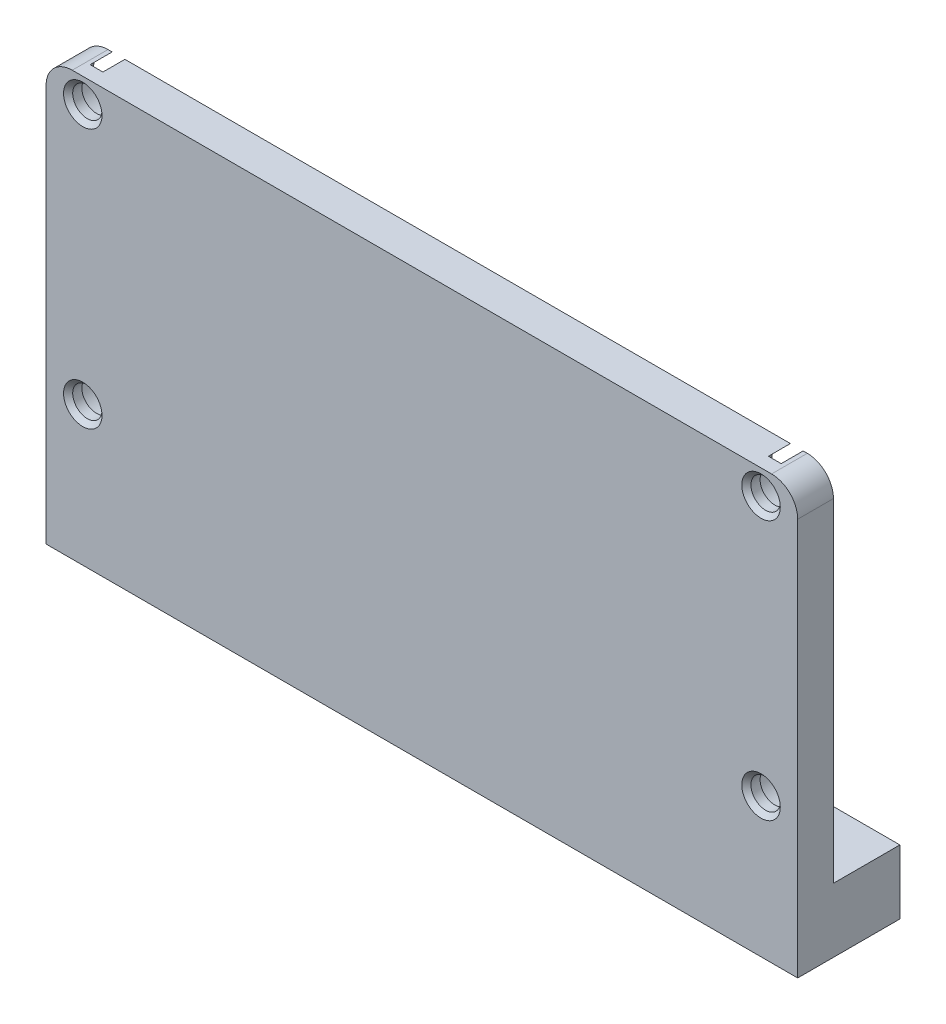
SolidWorks part; units mm, degrees
ref_plane "Front Plane" through (0, 0, 0) normal (0, 0, 1) x (1, 0, 0)
ref_plane "Top Plane" through (0, 0, 0) normal (0, 1, 0) x (1, 0, 0)
ref_plane "Right Plane" through (0, 0, 0) normal (1, 0, 0) x (0, 0, -1)
sketch "Sketch1" plane through (0, 0, 0) normal (0, 0, 1) x (1, 0, 0)
  line L1 (81, 11.6) -> (1, 11.6) construction
  line L3 (0, -35.2) -> (82, -35.2)
  line L5 (79.15, 11.6) -> (2.85, 11.6)
  line L9 (82, -35.2) -> (82, 8.75)
  line L10 (0, 8.75) -> (0, -35.2)
  line L11 (4, 8.9396) -> (4, -41.6656) construction
  circle A0 centre (4, 8.9396) radius 1.6 construction
  circle A1 centre (78, 8.9396) radius 1.6 construction
  circle A2 centre (4, -29.89) radius 1.6 construction
  circle A3 centre (4, 8.9396) radius 1.6
  circle A4 centre (78, 8.9396) radius 1.6
  arc A5 (82, 8.75) -> (79.15, 11.6) centre (79.15, 8.75) ccw
  arc A6 (0, 8.75) -> (2.85, 11.6) centre (2.85, 8.75) cw
  dimension "D1" = 46.8
  dimension "D2" = 2.85
extrude "Boss-Extrude1" add sketch "Sketch1" along normal blind 11.15 contours A3
sketch "Sketch2" plane through (0, 0, 0) normal (0, 0, -1) x (-1, 0, 0)
  line L0 (0, -49.6) -> (-82, -49.6) construction
  line L1 (0, -49.6) -> (-82, -49.6) construction
  line L2 (-82, -54.6) -> (0, -54.6)
  line L3 (-82, -34.6) -> (0, -34.6)
  line L4 (-82, -35.2) -> (-82, 8.75) construction
  line L5 (0, 8.75) -> (0, -35.2) construction
  line L7 (0, -34.6) -> (0, -35.2)
  line L8 (-82, -35.2) -> (-82, -34.6)
  line L9 (-82, -35.2) -> (0, -35.2)
  dimension "D1" = 5
  dimension "D2" = 20
extrude "Cut-Extrude1" cut sketch "Sketch2" against normal blind 8 contours L3 L7 L9 L8
sketch "Sketch3" plane through (0, -34.6, 0) normal (0, -1, 0) x (1, 0, 0)
  line L0 (10.85, 4) -> (10.85, 0)
  line L1 (14.15, 4) -> (14.15, 0)
  line L2 (16.75, 4) -> (16.75, 0)
  line L3 (23.25, 4) -> (23.25, 0)
  line L4 (0, 0) -> (82, 0)
  line L5 (82, 0) -> (82, 8)
  line L6 (82, 8) -> (0, 8)
  line L7 (0, 8) -> (0, 0)
  line L8 (10.85, 0) -> (14.15, 0)
  line L9 (82, 0) -> (82, 8)
  line L10 (82, 8) -> (0, 8)
  line L11 (0, 8) -> (0, 0)
  line L12 (25.85, 4) -> (25.85, 0)
  line L13 (29.15, 4) -> (29.15, 0)
  line L14 (25.85, 0) -> (82, 0)
  line L15 (16.75, 0) -> (23.25, 0)
  arc A0 (14.15, 4) -> (10.85, 4) centre (12.5, 4) ccw
  arc A1 (23.25, 4) -> (16.75, 4) centre (20, 4) ccw
  arc A2 (29.15, 4) -> (25.85, 4) centre (27.5, 4) ccw
  line M5 (0, 0) -> (82, 0)
  dimension "D2" = 3.3
  dimension "D3" = 3.3
  dimension "D4" = 15
  dimension "D5" = 7.5
  dimension "D6" = 6.5
  dimension "D7" = 20
  dimension "D1" = 0
extrude "Cut-Extrude2" cut sketch "Sketch3" against normal up to next (46.2 mm away) contours L13 A2 L12 M5 | A0 L0 L8 L1 | A1 L2 L15 L3
sketch "Sketch4" plane through (0, 11.6, 0) normal (0, 1, 0) x (1, 0, 0)
  line L0 (9.25, -4) -> (9.25, 0)
  line L1 (10.85, 0) -> (2.85, 0) construction
  line L2 (15.75, -4) -> (15.75, 0)
  line L3 (16.75, 0) -> (14.15, 0) construction
  line L4 (15.75, 0) -> (9.25, 0)
  line L5 (24.25, -4) -> (24.25, 0)
  line L6 (25.85, 0) -> (23.25, 0) construction
  line L7 (24.25, 0) -> (30.75, 0)
  line L8 (79.15, 0) -> (29.15, 0) construction
  line L9 (30.75, 0) -> (30.75, -4)
  arc A0 (10.85, -4) -> (14.15, -4) centre (12.5, -4) ccw construction
  arc A1 (25.85, -4) -> (29.15, -4) centre (27.5, -4) ccw construction
  arc A2 (10.85, -4) -> (14.15, -4) centre (12.5, -4) ccw construction
  arc A3 (25.85, -4) -> (29.15, -4) centre (27.5, -4) ccw construction
  arc A4 (9.25, -4) -> (15.75, -4) centre (12.5, -4) ccw
  arc A5 (24.25, -4) -> (30.75, -4) centre (27.5, -4) ccw
  dimension "D1" = 6.5
  dimension "D2" = 6.5
extrude "Cut-Extrude3" cut sketch "Sketch4" against normal offset from surface (40.2 mm away) 6 up to face at (25.25, -34.6, 2.9094)
sketch "Sketch6" plane through (0, 11.6, 0) normal (0, 1, 0) x (1, 0, 0)
  line L0 (15.75, -4) -> (15.75, 0) construction
  line L1 (24.25, 0) -> (24.25, -4) construction
  line L2 (15.75, -4) -> (15.75, 0)
  line L3 (24.25, 0) -> (24.25, -4)
  line L4 (12.5, -7.25) -> (0, -7.25)
  line L6 (0, -7.25) -> (0, 1.0612)
  line L7 (0, 1.0612) -> (15.75, 1.0612)
  line L8 (15.75, 1.0612) -> (15.75, 0)
  line L9 (27.5, -7.25) -> (41, -7.25)
  line L10 (41, -7.25) -> (41, 0)
  line L11 (79.15, 0) -> (30.75, 0) construction
  line L12 (41, 0) -> (24.25, 0)
  arc A0 (9.25, -4) -> (15.75, -4) centre (12.5, -4) ccw construction
  arc A1 (24.25, -4) -> (30.75, -4) centre (27.5, -4) ccw construction
  arc A2 (12.5, -7.25) -> (15.75, -4) centre (12.5, -4) ccw
  arc A3 (24.25, -4) -> (27.5, -7.25) centre (27.5, -4) ccw
  dimension "D1" = 41
extrude "Cut-Extrude5" cut sketch "Sketch6" against normal offset from surface (39.2 mm away) 7 up to face at (25.25, -34.6, 2.9094)
ref_plane "Plane1" through (41, 0, 0) normal (-1, 0, 0) x (0, 0, 1)
mirror "Mirror1" about plane through (41, 0, 0) normal (-1, 0, 0) of "Cut-Extrude5", "Cut-Extrude3", "Cut-Extrude2", "Cut-Extrude1"
sketch "Sketch8" plane through (0, 0, 8) normal (0, 0, -1) x (-1, 0, 0)
  line L4 (-82, -34.6) -> (-82, -35.2)
  line L5 (-82, -35.2) -> (0, -35.2)
  line L6 (0, -35.2) -> (0, -34.6)
  line L7 (0, -34.6) -> (-82, -34.6)
  line L8 (-82, -34.6) -> (-82, -35.2)
  line L9 (-82, -35.2) -> (0, -35.2)
  line L10 (0, -35.2) -> (0, -34.6)
  line L11 (0, -34.6) -> (-82, -34.6)
  dimension "D1" = 0
sketch "Sketch9" plane through (0, 0, 0) normal (-1, 0, 0) x (0, 0, 1)
  line L2 (7.25, 11.6) -> (0, 2.4)
  line L3 (0, 11.6) -> (7.25, 11.6)
sketch "Sketch12" plane through (0, 11.6, 0) normal (0, 1, 0) x (1, 0, 0)
  line L0 (16.75, -4) -> (16.75, 0)
  line L1 (16.75, 0) -> (18, 0)
  line L2 (23.25, 0) -> (23.25, -4)
  line L5 (22, 0) -> (23.25, 0)
  line L6 (58.75, -4) -> (58.75, 0)
  line L7 (58.75, 0) -> (60.05, 0)
  line L8 (65.25, 0) -> (65.25, -4) construction
  line L9 (65.25, 0) -> (65.25, -4)
  line L10 (60.05, 0) -> (60.155, -3.1064)
  line L11 (18, 0) -> (18.11, -3.0846)
  line L12 (63.95, 0) -> (65.25, 0)
  line L13 (22, 0) -> (21.89, -3.0846)
  line L15 (63.95, 0) -> (63.845, -3.1064)
  arc A0 (16.75, -4) -> (23.25, -4) centre (20, -4) ccw construction
  arc A1 (58.75, -4) -> (65.25, -4) centre (62, -4) ccw construction
  arc A2 (16.75, -4) -> (23.25, -4) centre (20, -4) ccw
  arc A3 (58.75, -4) -> (65.25, -4) centre (62, -4) ccw
  arc A4 (18.11, -3.0846) -> (21.89, -3.0846) centre (20, -4) ccw
  arc A5 (60.155, -3.1064) -> (63.845, -3.1064) centre (62, -4) ccw
  dimension "D1" = 1.25
  dimension "D2" = 4.1
  dimension "D3" = 1.3
  dimension "D4" = 1.3
  dimension "D5" = 1.25
extrude "Boss-Extrude2" add sketch "Sketch12" against normal offset from surface (32.2 mm away) 7 up to face at (41, -27.6, 3.9744)
chamfer "Chamfer3" distance 1.1 angle 45 3 edges at (58.75, -20.6, 2) (65.25, -20.6, 2) (62, -20.6, 7.25)
chamfer "Chamfer4" distance 1.1 angle 45 3 edges at (16.75, -20.6, 2) (23.25, -20.6, 2) (20, -20.6, 7.25)
extrude "Cut-Extrude12" cut sketch "Sketch9" against normal through all and the other way through all flip side to cut contours L3 L2
fillet "Fillet3" radius 15 2 edges at (16.875, 2.4, 0) (23.125, 2.4, 0)
sketch "Sketch13" plane through (0, 0, 7.25) normal (0, 0, -1) x (-1, 0, 0)
  circle A0 centre (-78, 8.9396) radius 2.85
  dimension "D1" = 5.7
sketch "Sketch14" plane through (0, 0, 11.15) normal (0, 0, 1) x (1, 0, 0)
  circle A0 centre (4, -19.4004) radius 1.6 construction
  circle A1 centre (4, -19.4004) radius 1.6
extrude "Cut-Extrude14" cut sketch "Sketch14" against normal through all contours A1
mirror "Mirror3" about plane through (41, 0, 0) normal (-1, 0, 0) of "Cut-Extrude14"
sketch "Sketch18" plane through (0, -27.6, 0) normal (0, 1, 0) x (1, 0, 0)
  line L6 (14.15, 0) -> (14.15, -4)
  line L7 (10.85, -4) -> (10.85, 0)
  line L8 (10.85, 0) -> (9.25, 0)
  line L9 (9.25, 0) -> (9.25, -4)
  line L10 (15.75, -4) -> (15.75, 0)
  line L11 (15.75, 0) -> (14.15, 0)
  line L12 (14.15, 0) -> (14.15, -1.2)
  line L13 (10.85, -1.2) -> (10.85, 0)
  line L14 (10.85, 0) -> (9.25, 0)
  line L15 (9.25, 0) -> (9.25, -4)
  line L16 (15.75, -4) -> (15.75, 0)
  line L17 (15.75, 0) -> (14.15, 0)
  line L18 (29.15, 0) -> (29.15, -4)
  line L19 (25.85, -4) -> (25.85, 0)
  line L20 (25.85, 0) -> (24.25, 0)
  line L21 (24.25, 0) -> (24.25, -4)
  line L22 (30.75, -4) -> (30.75, 0)
  line L23 (30.75, 0) -> (29.15, 0)
  line L24 (29.15, 0) -> (29.15, -1.2)
  line L25 (25.85, -1.2) -> (25.85, 0)
  line L26 (25.85, 0) -> (24.25, 0)
  line L27 (24.25, 0) -> (24.25, -4)
  line L28 (30.75, -4) -> (30.75, 0)
  line L29 (30.75, 0) -> (29.15, 0)
  arc A0 (10.85, -1.2) -> (9.25, -4) centre (12.5, -4) ccw
  arc A1 (15.75, -4) -> (14.15, -1.2) centre (12.5, -4) ccw
  arc A2 (10.85, -4) -> (14.15, -4) centre (12.5, -4) ccw
  arc A3 (9.25, -4) -> (15.75, -4) centre (12.5, -4) ccw
  arc A4 (25.85, -1.2) -> (24.25, -4) centre (27.5, -4) ccw
  arc A5 (30.75, -4) -> (29.15, -1.2) centre (27.5, -4) ccw
  arc A6 (25.85, -4) -> (29.15, -4) centre (27.5, -4) ccw
  arc A7 (24.25, -4) -> (30.75, -4) centre (27.5, -4) ccw
  dimension "D1" = 0
  dimension "D2" = 0
extrude "Boss-Extrude3" add sketch "Sketch18" against normal blind 3.5
mirror "Mirror5" about plane through (41, 0, 0) normal (-1, 0, 0) of "Boss-Extrude3"
sketch "Sketch19" plane through (0, 0, 7.25) normal (0, 0, -1) x (-1, 0, 0)
  circle A0 centre (-78, -19.4004) radius 2.85
extrude "Cut-Extrude16" cut sketch "Sketch8" against normal through all contours L11 L8 L9 L10
sketch "Sketch20" plane through (0, 0, 7.25) normal (0, 0, -1) x (-1, 0, 0)
  circle A0 centre (-78, 8.9396) radius 2.75
  circle A1 centre (-78, -19.4004) radius 2.75
  dimension "D1" = 5.5
extrude "Cut-Extrude17" cut sketch "Sketch20" against normal blind 2.4
mirror "Mirror7" about plane through (41, 0, 0) normal (-1, 0, 0) of "Cut-Extrude17"
chamfer "Chamfer5" distance 0.5 angle 45 4 edges at (79.6, 8.9396, 11.15) (76.4, -19.4004, 11.15) (5.6, -19.4004, 11.15) (5.6, 8.9396, 11.15)
